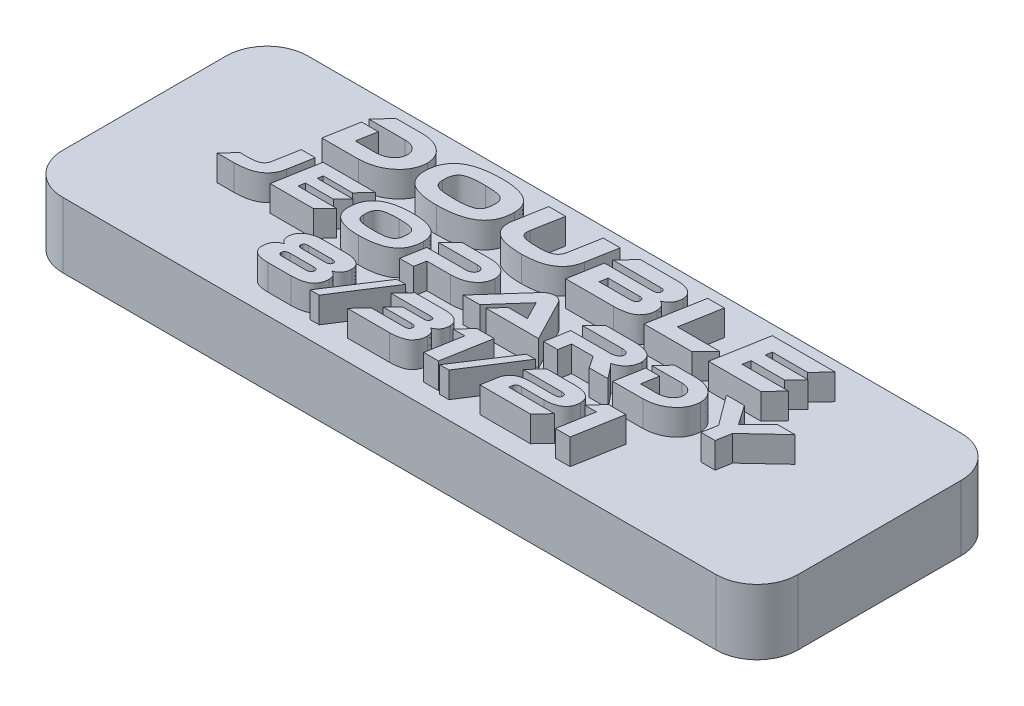
SolidWorks part; units mm, degrees
ref_plane "Front Plane" through (0, 0, 0) normal (0, 0, 1) x (1, 0, 0)
ref_plane "Top Plane" through (0, 0, 0) normal (0, 1, 0) x (1, 0, 0)
ref_plane "Right Plane" through (0, 0, 0) normal (1, 0, 0) x (0, 0, -1)
sketch "Sketch1" plane through (0, 0, 0) normal (0, 1, 0) x (1, 0, 0)
  line L1 (-28.575, 9.525) -> (28.575, 9.525)
  line L2 (-28.575, 9.525) -> (-28.575, -9.525)
  line L3 (-28.575, -9.525) -> (28.575, -9.525)
  line L4 (28.575, 9.525) -> (28.575, -9.525)
  line L5 (-28.575, 9.525) -> (28.575, -9.525) construction
  line L6 (-28.575, -9.525) -> (28.575, 9.525) construction
  point P0 (0, 0)
  dimension "D1" = 57.15
  dimension "D2" = 19.05
extrude "Boss-Extrude1" add sketch "Sketch1" along normal up to surface (5.08 mm away)
fillet "Fillet1" radius 3.175 4 edges at (-28.575, 2.54, 9.525) (-28.575, 2.54, -9.525) (28.575, 2.54, 9.525) (28.575, 2.54, -9.525)
sketch "Sketch3" plane through (0, 5.08, 0) normal (0, 1, 0) x (1, 0, 0)
  line L0 (28.575, -7.9375) -> (-28.575, -7.9375) construction
  line L1 (28.575, -6.35) -> (28.575, 6.35) construction
  line L2 (-28.575, 6.35) -> (-28.575, -6.35) construction
  line L3 (28.575, 2.54) -> (-28.575, 2.54) construction
  line L4 (-28.575, -2.54) -> (28.575, -2.54) construction
  line L5 (-25.4, -9.525) -> (25.4, -9.525) construction
  line L6 (25.4, 9.525) -> (-25.4, 9.525) construction
  line L7 (28.575, 2.54) -> (28.575, -2.54) construction
  text T0 "Double\r\n\r\n\r\n" font "Ethnocentric Rg" height in points 16
  text T1 "8/31/21" font "Ethnocentric Rg" height in points 14
  text T2 "jeopardy" font "Ethnocentric Rg" height 3.5
  point P11 (28.575, 0)
  point P13 (28.575, 0)
  dimension "D1" = 1.5875
  dimension "D2" = 5.08
extrude "Boss-Extrude2" add sketch "Sketch3" along normal blind 2
sketch "Sketch4" plane through (0, 0, 0) normal (0, -1, 0) x (1, 0, 0)
  line L0 (25.4, 0) -> (-25.4, 0) construction
  circle A0 centre (-25.4, 0) radius 0.9
  circle A1 centre (25.4, 0) radius 0.9
  point P3 (0, 0)
  dimension "D2" = 1.8
  dimension "D1" = 50.8
extrude "Cut-Extrude1" cut sketch "Sketch4" against normal blind 4
